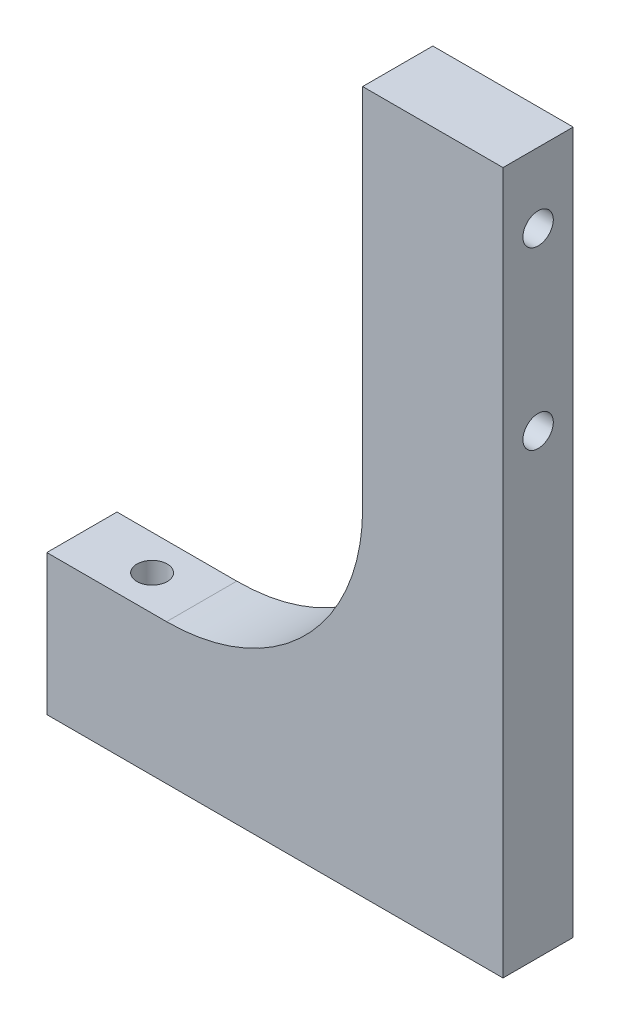
SolidWorks part; units mm, degrees
ref_plane "Front Plane" through (0, 0, 0) normal (0, 0, 1) x (1, 0, 0)
ref_plane "Top Plane" through (0, 0, 0) normal (0, 1, 0) x (1, 0, 0)
ref_plane "Right Plane" through (0, 0, 0) normal (1, 0, 0) x (0, 0, -1)
sketch "Sketch1" plane through (0, 0, 0) normal (0, 0, 1) x (1, 0, 0)
  line L0 (0, 194.7318) -> (0, -59.2682)
  line L1 (0, -59.2682) -> (-165.1, -59.2682)
  line L2 (-165.1, -59.2682) -> (-165.1, -8.4682)
  line L3 (-165.1, -8.4682) -> (-50.8, -8.4682)
  line L4 (-50.8, -8.4682) -> (-50.8, 194.7318)
  line L5 (-50.8, 194.7318) -> (0, 194.7318)
  dimension "D1" = 254
  dimension "D2" = 165.1
  dimension "D3" = 50.8
  dimension "D4" = 50.8
extrude "Boss-Extrude1" add sketch "Sketch1" along normal blind 25.4
sketch "Sketch2" plane through (-50.8, 0, 0) normal (-1, 0, 0) x (0, 0, 1)
  line L0 (25.4, 194.7318) -> (0, 194.7318) construction
  line L1 (0, 194.7318) -> (25.4, 194.7318)
  line L2 (0, 194.7318) -> (0, -8.4682)
  line L3 (0, -8.4682) -> (25.4, -8.4682)
  line L4 (25.4, 194.7318) -> (25.4, -8.4682)
  line L5 (0, 194.7318) -> (25.4, -8.4682) construction
  line L6 (0, -8.4682) -> (25.4, 194.7318) construction
  line L7 (0, 194.7318) -> (0, -8.4682) construction
  circle A0 centre (12.7, 105.8318) radius 2.54
  circle A1 centre (12.7, 169.3318) radius 2.54
  point P0 (12.7, 93.1318)
  dimension "D1" = 25.4
  dimension "D2" = 63.5
sketch "Sketch3" plane through (0, -8.4682, 0) normal (0, 1, 0) x (1, 0, 0)
  line L0 (-165.1, -25.4) -> (-165.1, 0) construction
  line L1 (-50.8, 0) -> (-165.1, 0) construction
  circle A0 centre (-139.7, -12.7) radius 2.54
  dimension "D1" = 25.4
  dimension "D3" = 12.7
hole_wizard "M10 Clearance Hole1" positions "Sketch4" profile "Sketch5" hole size "M10" standard "ANSI Metric" end condition through all
sketch "Sketch4" plane through (0, -8.4682, 0) normal (0, 1, 0) x (1, 0, 0)
  point P0 (-139.7, -12.7)
sketch "Sketch5" plane through (-139.7, -8.4682, 12.7) normal (1, 0, 0) x (0, 0, 1)
  line L0 (0, 0) -> (0, 50.8)
  line L1 (0, 50.8) -> (5.5, 50.8)
  line L2 (5.5, 50.8) -> (5.5, 0)
  line L5 (5.5, 0) -> (0, 0)
  line L11 (0, -6.35) -> (0, 107.95) construction
  dimension "Thru Hole Dia." = 11
  dimension "Thru Hole Depth" = 50.8
hole_wizard "M10 Clearance Hole2" positions "Sketch6" profile "Sketch7" hole size "M10" standard "ANSI Metric" end condition through all
sketch "Sketch6" plane through (-50.8, 0, 0) normal (-1, 0, 0) x (0, 0, 1)
  point P0 (12.7, 169.3318)
  point P3 (12.7, 105.8318)
sketch "Sketch7" plane through (-50.8, 169.3318, 12.7) normal (0, 1, 0) x (0, 0, 1)
  line L0 (0, 0) -> (0, 50.8)
  line L1 (0, 50.8) -> (5.5, 50.8)
  line L2 (5.5, 50.8) -> (5.5, 0)
  line L5 (5.5, 0) -> (0, 0)
  line L11 (0, -6.35) -> (0, 107.95) construction
  dimension "Thru Hole Dia." = 11
  dimension "Thru Hole Depth" = 50.8
fillet "Fillet1" radius 70.96 1 edges at (-50.8, -8.4682, 12.7)
